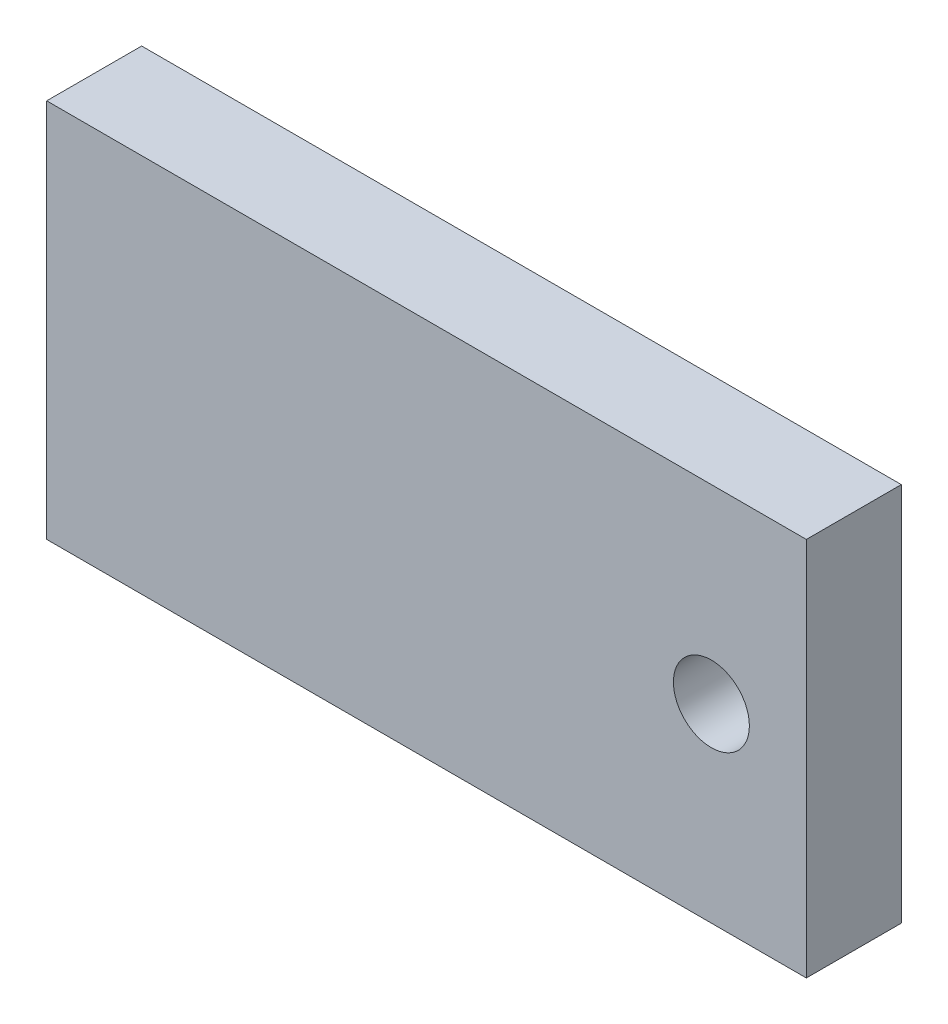
SolidWorks part; units mm, degrees
ref_plane "前视基准面" through (0, 0, 0) normal (0, 0, 1) x (1, 0, 0)
ref_plane "上视基准面" through (0, 0, 0) normal (0, 1, 0) x (1, 0, 0)
ref_plane "右视基准面" through (0, 0, 0) normal (1, 0, 0) x (0, 0, -1)
sketch "草图1" plane through (0, 0, 0) normal (0, 0, 1) x (1, 0, 0)
  line L0 (-29.3007, 22.6112) -> (-29.3007, 2.6112)
  line L1 (-29.3007, 2.6112) -> (0.6993, 2.6112)
  line L2 (0.6993, 2.6112) -> (10.6993, 2.6112)
  line L3 (10.6993, 2.6112) -> (10.6993, 22.6112)
  line L4 (10.6993, 22.6112) -> (-29.3007, 22.6112)
  line L5 (10.6993, 12.6112) -> (5.6993, 12.6112) construction
  circle A0 centre (5.6993, 12.6112) radius 2
  dimension "D5" = 4
  dimension "D1" = 20
  dimension "D2" = 30
  dimension "D3" = 10
  dimension "D4" = 5
extrude "凸台-拉伸1" add sketch "草图1" along normal blind 5
